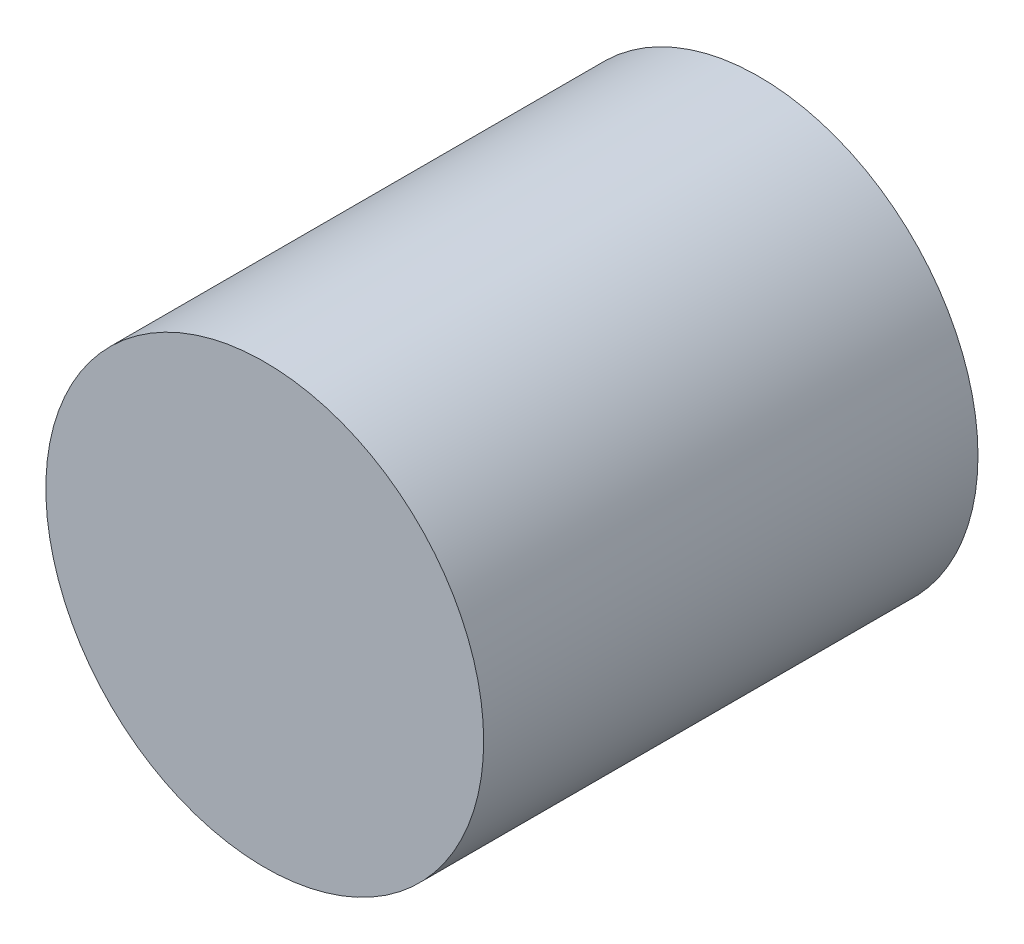
SolidWorks part; units mm, degrees
ref_plane "Front Plane" through (0, 0, 0) normal (0, 0, 1) x (1, 0, 0)
ref_plane "Top Plane" through (0, 0, 0) normal (0, 1, 0) x (1, 0, 0)
ref_plane "Right Plane" through (0, 0, 0) normal (1, 0, 0) x (0, 0, -1)
sketch "Sketch1" plane through (0, 0, 0) normal (0, 0, 1) x (1, 0, 0)
  circle A0 centre (0, 0) radius 1.55
  dimension "D1" = 3.1
extrude "Boss-Extrude1" add sketch "Sketch1" along normal blind 3.5
